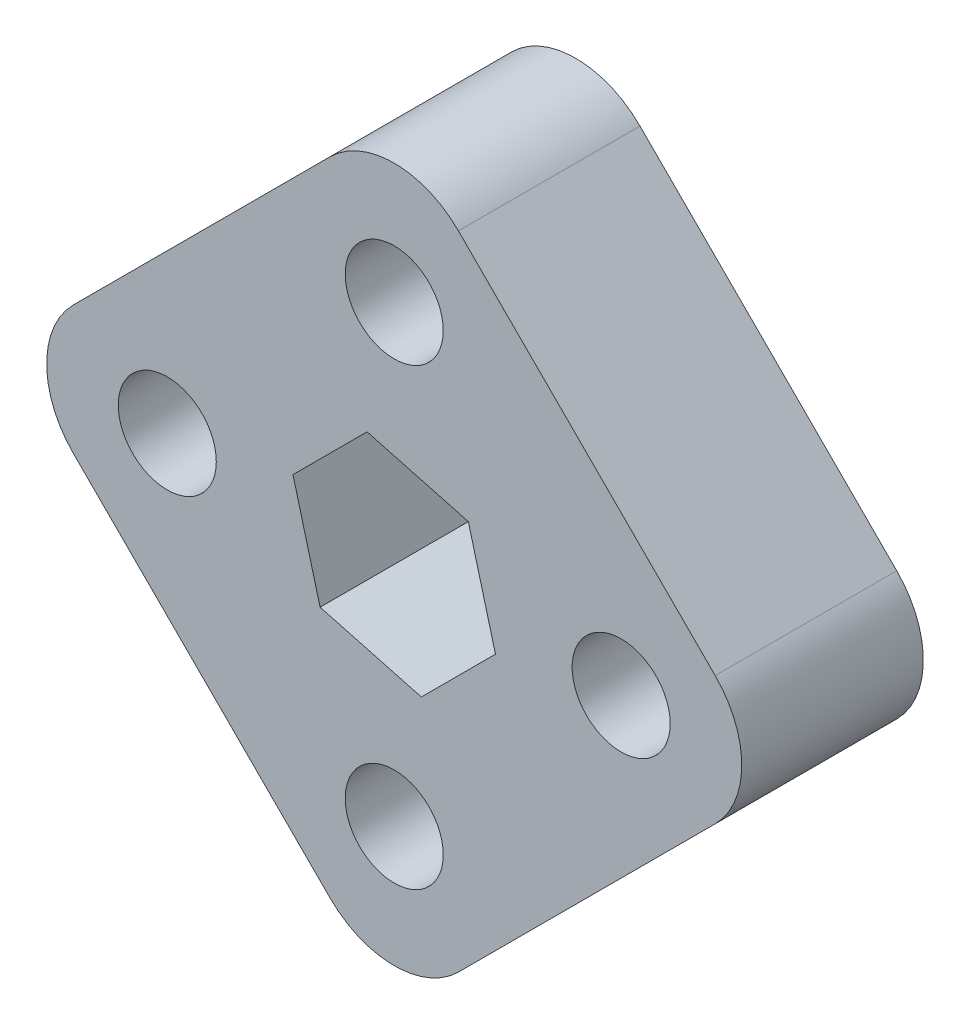
SolidWorks part; units mm, degrees
ref_plane "Front Plane" through (0, 0, 0) normal (0, 0, 1) x (1, 0, 0)
ref_plane "Top Plane" through (0, 0, 0) normal (0, 1, 0) x (1, 0, 0)
ref_plane "Right Plane" through (0, 0, 0) normal (1, 0, 0) x (0, 0, -1)
sketch "Sketch2" plane through (0, 0, 0) normal (0, 0, 1) x (1, 0, 0)
  line L0 (0, -29.6348) -> (0, 29.6348) construction
  line L1 (5.1848, 5.1848) -> (-1.8978, 7.0825)
  line L2 (-1.8978, 7.0825) -> (-7.0825, 1.8978)
  line L3 (-7.0825, 1.8978) -> (-5.1848, -5.1848)
  line L4 (-5.1848, -5.1848) -> (1.8978, -7.0825)
  line L5 (1.8978, -7.0825) -> (7.0825, -1.8978)
  line L6 (7.0825, -1.8978) -> (5.1848, 5.1848)
  line L7 (0, 0) -> (0, 15.875) construction
  line L8 (-4.4901, 22.4506) -> (-22.4506, 4.4901)
  line L9 (29.6348, 0) -> (-29.6348, 0) construction
  line L10 (-22.4506, -4.4901) -> (-4.4901, -22.4506)
  line L11 (4.4901, -22.4506) -> (22.4506, -4.4901)
  line L12 (22.4506, 4.4901) -> (4.4901, 22.4506)
  line L13 (0, 26.9408) -> (0, -26.9408) construction
  line L14 (-26.9408, 0) -> (26.9408, 0) construction
  circle A0 centre (0, 0) radius 6.35 construction
  circle A1 centre (0, 15.875) radius 3.429
  circle A2 centre (15.875, 0) radius 3.429
  circle A3 centre (0, -15.875) radius 3.429
  circle A4 centre (-15.875, 0) radius 3.429
  circle A6 centre (0, 0) radius 15.875 construction
  arc A7 (-22.4506, 4.4901) -> (-22.4506, -4.4901) centre (-17.9605, 0) ccw
  arc A8 (-4.4901, -22.4506) -> (4.4901, -22.4506) centre (0, -17.9605) ccw
  arc A9 (22.4506, -4.4901) -> (22.4506, 4.4901) centre (17.9605, 0) ccw
  arc A10 (4.4901, 22.4506) -> (-4.4901, 22.4506) centre (0, 17.9605) ccw
  point P14 (0, 0)
  point P41 (-2.0641, 7.0358)
  dimension "D1" = 12.7
  dimension "D3" = 15.875
  dimension "D4" = 6.858
  dimension "D6" = 38.1
  dimension "D7" = 6.35
  dimension "D5" = 4
extrude "Boss-Extrude1" add sketch "Sketch2" along normal blind 12.7
